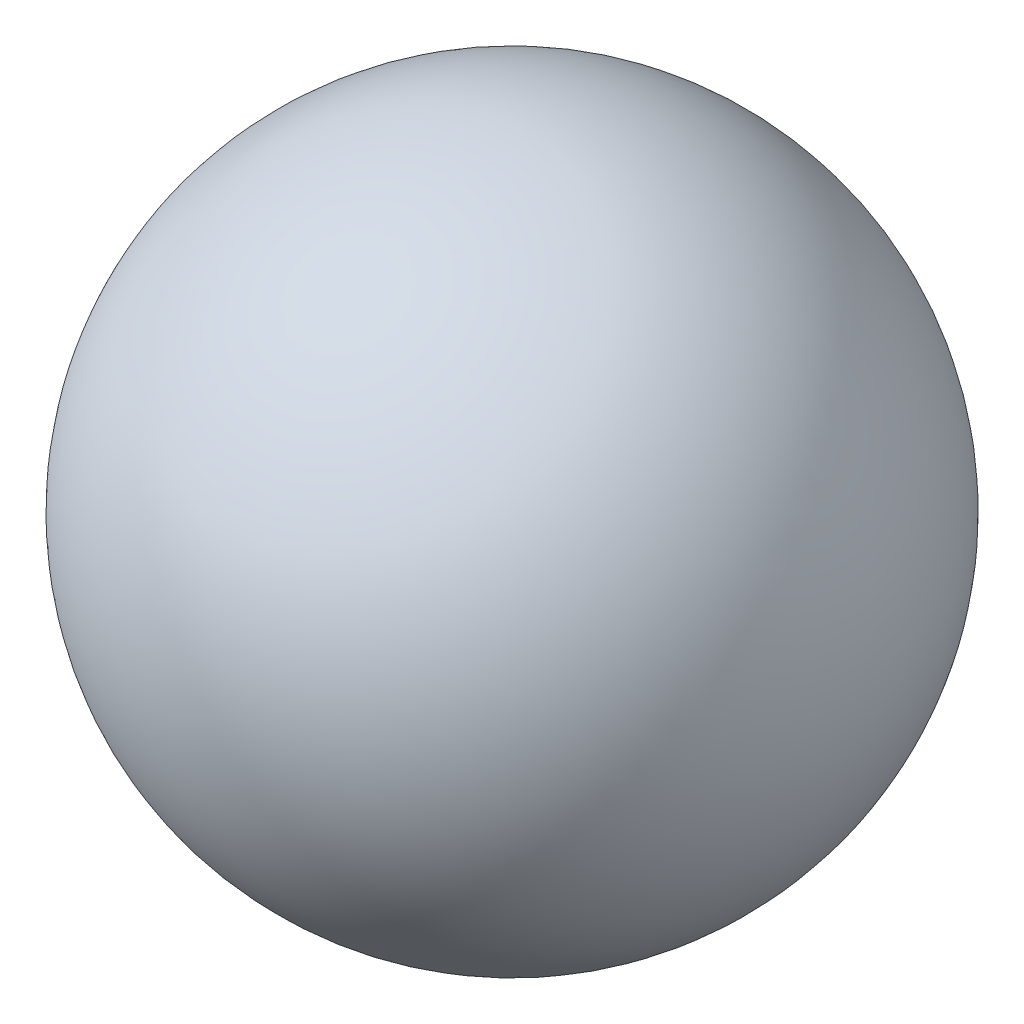
SolidWorks part; units mm, degrees
ref_plane "Ön Düzlem" through (0, 0, 0) normal (0, 0, 1) x (1, 0, 0)
ref_plane "Üst Düzlem" through (0, 0, 0) normal (0, 1, 0) x (1, 0, 0)
ref_plane "Sağ Düzlem" through (0, 0, 0) normal (1, 0, 0) x (0, 0, -1)
sketch "Çizim1" plane through (0, 0, 0) normal (0, 0, 1) x (1, 0, 0)
  line L0 (1.5, 0) -> (-1.5, 0)
  arc A0 (1.5, 0) -> (-1.5, 0) centre (0, 0) ccw
  point P6 (0, 0)
  dimension "D1" = 3
revolve "Döndür1" add sketch "Çizim1" angle 360 about L0
